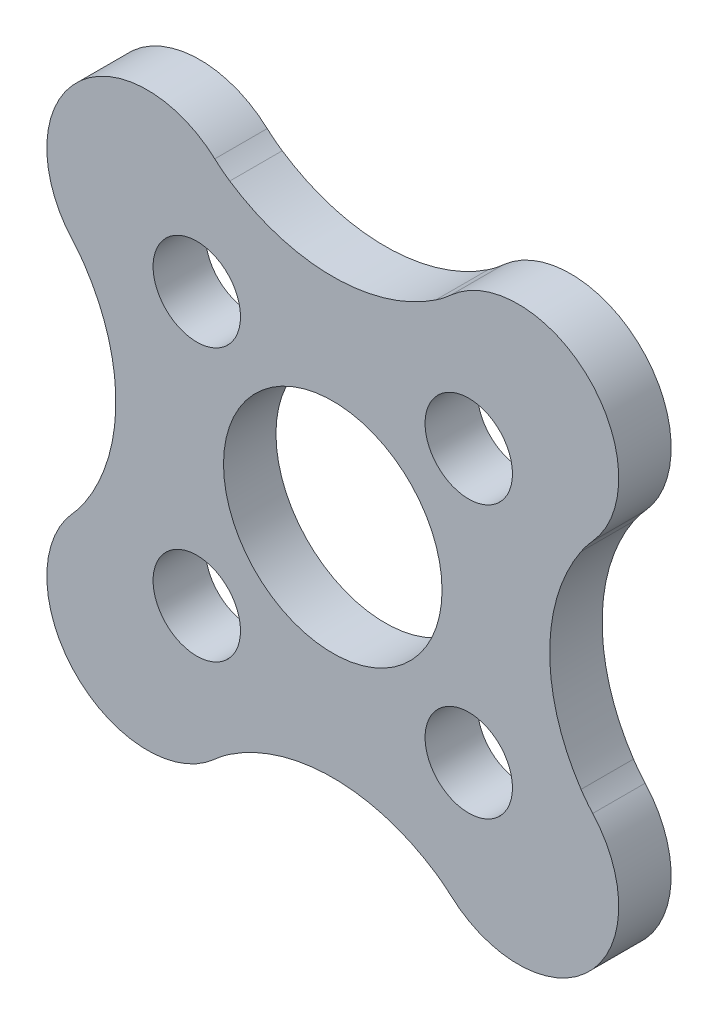
SolidWorks part; units mm, degrees
ref_plane "前视基准面" through (0, 0, 0) normal (0, 0, 1) x (1, 0, 0)
ref_plane "上视基准面" through (0, 0, 0) normal (0, 1, 0) x (1, 0, 0)
ref_plane "右视基准面" through (0, 0, 0) normal (1, 0, 0) x (0, 0, -1)
sketch "Model" plane through (0, 0, 0) normal (0, 0, 1) x (1, 0, 0)
  circle A0 centre (18.2961, 16.99) radius 1
  circle A1 centre (12.0735, 16.99) radius 1
  circle A2 centre (12.0735, 10.7674) radius 1
  circle A3 centre (18.2961, 10.7674) radius 1
  circle A4 centre (15.1848, 13.8787) radius 2.5
  arc A5 (12.4857, 19.8265) -> (12.8286, 19.5586) centre (14.499, 22.0506) ccw
  arc A6 (12.8286, 19.5586) -> (17.5409, 19.5586) centre (15.1848, 23.0737) ccw
  arc A7 (17.5409, 19.5586) -> (17.8839, 19.8265) centre (15.8706, 22.0506) ccw
  arc A8 (21.1326, 16.5778) -> (17.8839, 19.8265) centre (19.4274, 18.1213) ccw
  arc A9 (21.1326, 16.5778) -> (20.8647, 16.2348) centre (23.3567, 14.5645) ccw
  arc A10 (20.8647, 16.2348) -> (20.8647, 11.5226) centre (24.3798, 13.8787) ccw
  arc A11 (20.8647, 11.5226) -> (21.1326, 11.1796) centre (23.3567, 13.1929) ccw
  arc A12 (17.8839, 7.9309) -> (21.1326, 11.1796) centre (19.4274, 9.6361) ccw
  arc A13 (17.8839, 7.9309) -> (17.5409, 8.1988) centre (15.8706, 5.7068) ccw
  arc A14 (17.5409, 8.1988) -> (12.8286, 8.1988) centre (15.1848, 4.6837) ccw
  arc A15 (12.8286, 8.1988) -> (12.4857, 7.9309) centre (14.499, 5.7068) ccw
  arc A16 (12.4857, 19.8265) -> (9.237, 16.5778) centre (10.9421, 18.1213) ccw
  arc A17 (9.5049, 16.2348) -> (9.237, 16.5778) centre (7.0129, 14.5645) ccw
  arc A18 (9.5049, 11.5226) -> (9.5049, 16.2348) centre (5.9898, 13.8787) ccw
  arc A19 (9.237, 11.1796) -> (9.5049, 11.5226) centre (7.0129, 13.1929) ccw
  arc A20 (9.237, 11.1796) -> (12.4857, 7.9309) centre (10.9421, 9.6361) ccw
extrude "凸台-拉伸1" add sketch "Model" along normal blind 1.2 contours A5 A6 A7 A8 A9 A10 A11 A12 A13 A14 A15 A20 A19 A18 A17 A16 | A4 | A3 | A2 | A1 | A0
